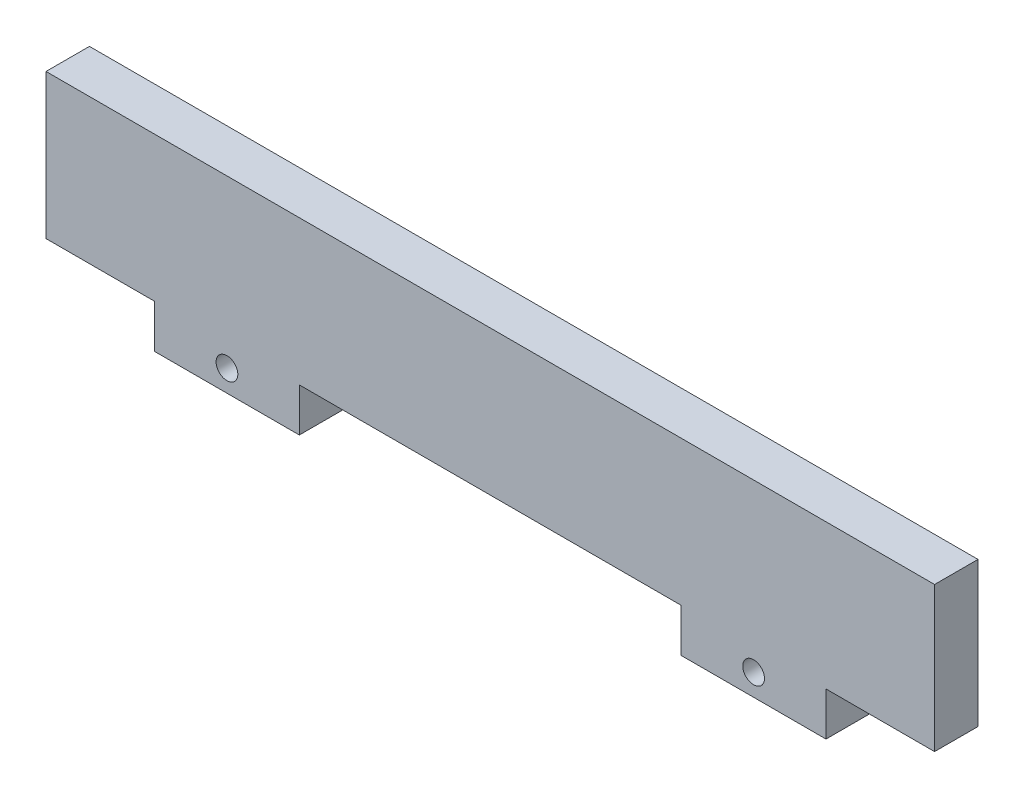
SolidWorks part; units mm, degrees
ref_plane "Plan de face" through (0, 0, 0) normal (0, 0, 1) x (1, 0, 0)
ref_plane "Plan de dessus" through (0, 0, 0) normal (0, 1, 0) x (1, 0, 0)
ref_plane "Plan de droite" through (0, 0, 0) normal (1, 0, 0) x (0, 0, -1)
sketch "Esquisse1" plane through (0, 0, 0) normal (0, 0, 1) x (1, 0, 0)
  line L1 (-61.38, 10) -> (61.38, 10)
  line L2 (-61.38, 10) -> (-61.38, -10)
  line L3 (-61.38, -10) -> (61.38, -10)
  line L4 (61.38, 10) -> (61.38, -10)
  dimension "D1" = 20
  dimension "D2" = 122.76
  dimension "D3" = 61.38
  dimension "D4" = 10
extrude "Boss.-Extru.1" add sketch "Esquisse1" along normal blind 6
sketch "Esquisse2" plane through (0, 0, 6) normal (0, 0, 1) x (1, 0, 0)
  line L0 (-61.38, -10) -> (61.38, -10) construction
  line L1 (-46.38, -10) -> (-26.38, -10)
  line L2 (-46.38, -10) -> (-46.38, -16)
  line L3 (-46.38, -16) -> (-26.38, -16)
  line L4 (-26.38, -10) -> (-26.38, -16)
  line L5 (-61.38, 10) -> (-61.38, -10) construction
  line L6 (26.38, -10) -> (46.38, -10)
  line L7 (26.38, -10) -> (26.38, -16)
  line L8 (26.38, -16) -> (46.38, -16)
  line L9 (46.38, -10) -> (46.38, -16)
  line L10 (61.38, -10) -> (61.38, 10) construction
  dimension "D1" = 6
  dimension "D2" = 20
  dimension "D3" = 20
  dimension "D4" = 6
  dimension "D5" = 15
  dimension "D6" = 15
extrude "Boss.-Extru.2" add sketch "Esquisse2" against normal blind 6
sketch "Esquisse3" plane through (0, 0, 6) normal (0, 0, 1) x (1, 0, 0)
  line L0 (-49.2744, -13) -> (58.6208, -13) construction
  line L1 (-46.38, -10) -> (-46.38, -16) construction
  line L2 (26.38, -10) -> (26.38, -16) construction
  line L3 (-46.38, -16) -> (-26.38, -16) construction
  circle A0 centre (-36.38, -13) radius 1.5
  circle A1 centre (36.38, -13) radius 1.5
  dimension "D1" = 3
  dimension "D3" = 3
  dimension "D4" = 10
  dimension "D2" = 10
  dimension "D5" = 3
extrude "Enlèv. mat.-Extru.1" cut sketch "Esquisse3" against normal blind 6
equation "\"D3@Esquisse1\"=\"D2@Esquisse1\"/2"
equation "\"D4@Esquisse1\"=\"D1@Esquisse1\"/2"
